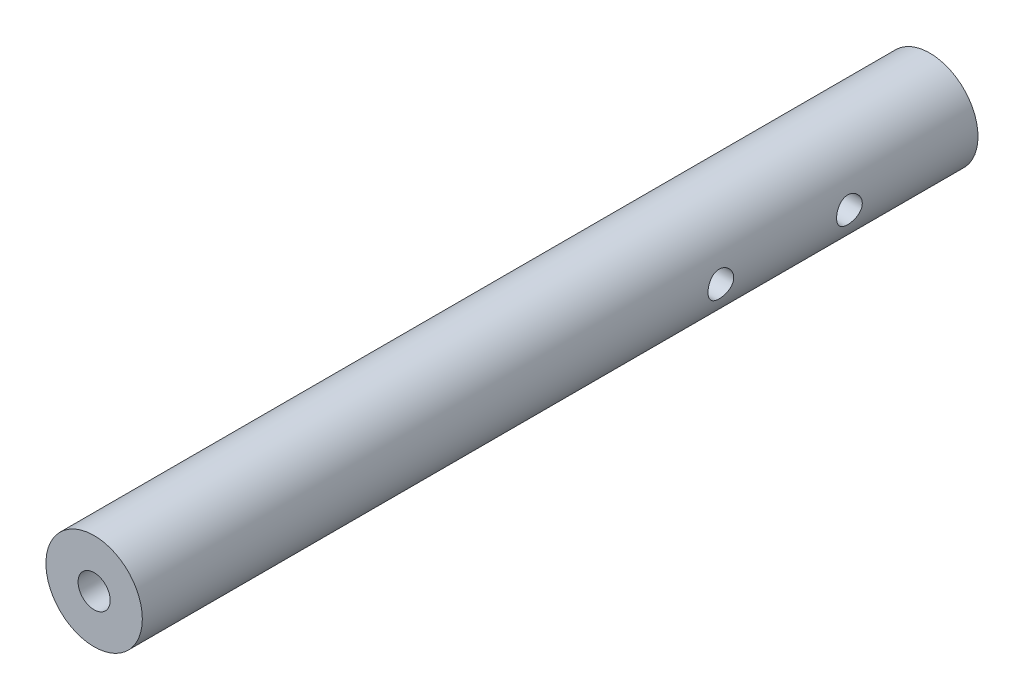
SolidWorks part; units mm, degrees
ref_plane "Front Plane" through (0, 0, 0) normal (0, 0, 1) x (1, 0, 0)
ref_plane "Top Plane" through (0, 0, 0) normal (0, 1, 0) x (1, 0, 0)
ref_plane "Right Plane" through (0, 0, 0) normal (1, 0, 0) x (0, 0, -1)
sketch "Sketch1" plane through (0, 0, 0) normal (0, 0, 1) x (1, 0, 0)
  circle A0 centre (0, 0) radius 7.5
  circle A1 centre (0, 0) radius 2.5
  dimension "D1" = 15
  dimension "D2" = 5
extrude "Boss-Extrude1" add sketch "Sketch1" along normal blind 130
ref_plane "Plane1" through (-7.5, 0, 0) normal (-1, 0, 0) x (0, 0, 1)
sketch "Sketch2" plane through (-7.5, 0, 0) normal (-1, 0, 0) x (0, 0, 1)
  line L0 (0, 0) -> (130, 0) construction
  line L1 (130, -7.5) -> (130, 7.5) construction
  circle A0 centre (20, 0) radius 2
  circle A1 centre (40, 0) radius 2
  dimension "D1" = 4
  dimension "D2" = 4
  dimension "D3" = 20
  dimension "D4" = 20
extrude "Cut-Extrude1" cut sketch "Sketch2" against normal blind 16
